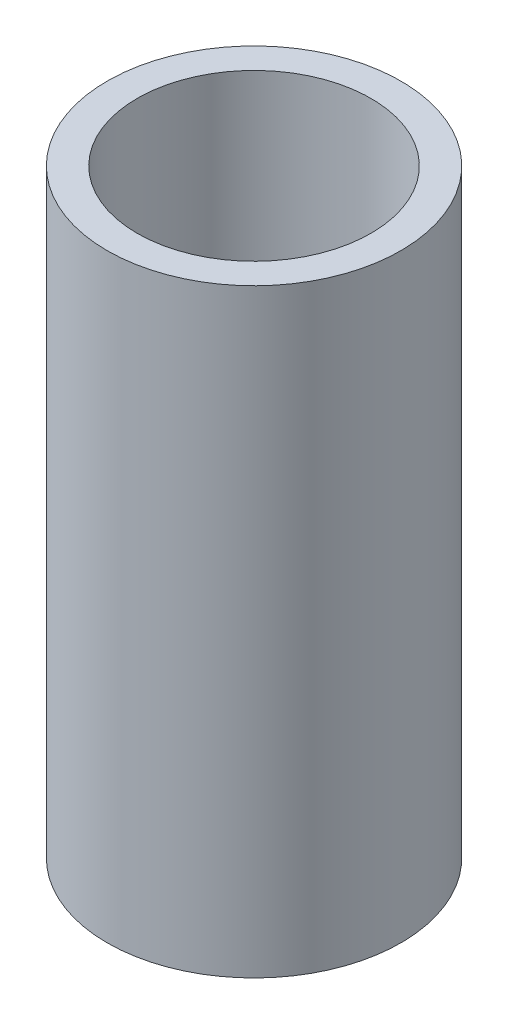
SolidWorks part; units mm, degrees
ref_plane "Front Plane" through (0, 0, 0) normal (0, 0, 1) x (1, 0, 0)
ref_plane "Top Plane" through (0, 0, 0) normal (0, 1, 0) x (1, 0, 0)
ref_plane "Right Plane" through (0, 0, 0) normal (1, 0, 0) x (0, 0, -1)
sketch "Sketch1" plane through (0, 0, 0) normal (0, 1, 0) x (1, 0, 0)
  circle A0 centre (0, 0) radius 24.5
  dimension "D1" = 49
extrude "Boss-Extrude1" add sketch "Sketch1" along normal blind 10
sketch "Sketch2" plane through (0, 10, 0) normal (0, 1, 0) x (1, 0, 0)
  circle A0 centre (0, 0) radius 24.5
  circle A1 centre (0, 0) radius 19.5
  dimension "D1" = 49
  dimension "D2" = 39
extrude "Boss-Extrude2" add sketch "Sketch2" along normal blind 90
